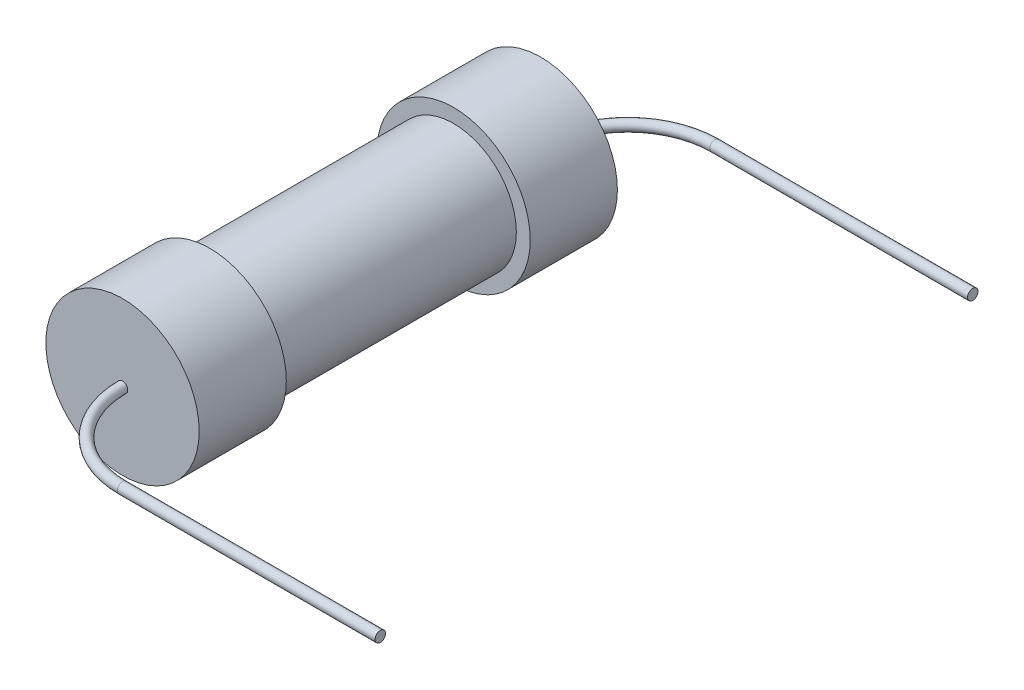
SolidWorks part; units mm, degrees
ref_plane "前视基准面" through (0, 0, 0) normal (0, 0, 1) x (1, 0, 0)
ref_plane "上视基准面" through (0, 0, 0) normal (0, 1, 0) x (1, 0, 0)
ref_plane "右视基准面" through (0, 0, 0) normal (1, 0, 0) x (0, 0, -1)
sketch "草图1" plane through (0, 0, 0) normal (0, 1, 0) x (1, 0, 0)
  line L1 (0.9, -1.75) -> (1.1, -1.75)
  line L2 (1.1, -1.75) -> (1.1, -3)
  line L3 (1.1, -3) -> (0, -3)
  line L4 (0, -3) -> (0, 3)
  line L5 (0, 3) -> (1.1, 3)
  line L6 (1.1, 3) -> (1.1, 1.75)
  line L7 (1.1, 1.75) -> (0.9, 1.75)
  line L8 (0.9, 1.75) -> (0.9, -1.75)
  line L9 (0, 0) -> (-1.8856, 0) construction
  dimension "D1" = 1.1
  dimension "D2" = 1.25
  dimension "D3" = 3.5
  dimension "D4" = 0.2
revolve "旋转1" add sketch "草图1" angle 360 about L4
sketch "草图6" plane through (0, 0, 0) normal (0, 1, 0) x (1, 0, 0)
  line L0 (1.1, 3) -> (-1.1, 3) construction
  line L1 (1.1, 3) -> (-1.1, 3) construction
  line L2 (1.25, 4.25) -> (4.9489, 4.25)
  arc A1 (1.25, 4.25) -> (0, 3) centre (1.25, 3) ccw
  dimension "D1" = 1.25
sweep "扫描1" add path "草图6" circular profile diameter 0.15 parameters "D3"=0.15
mirror "镜向1" about plane through (0, 0, 0) normal (0, 0, 1) of "扫描1"
